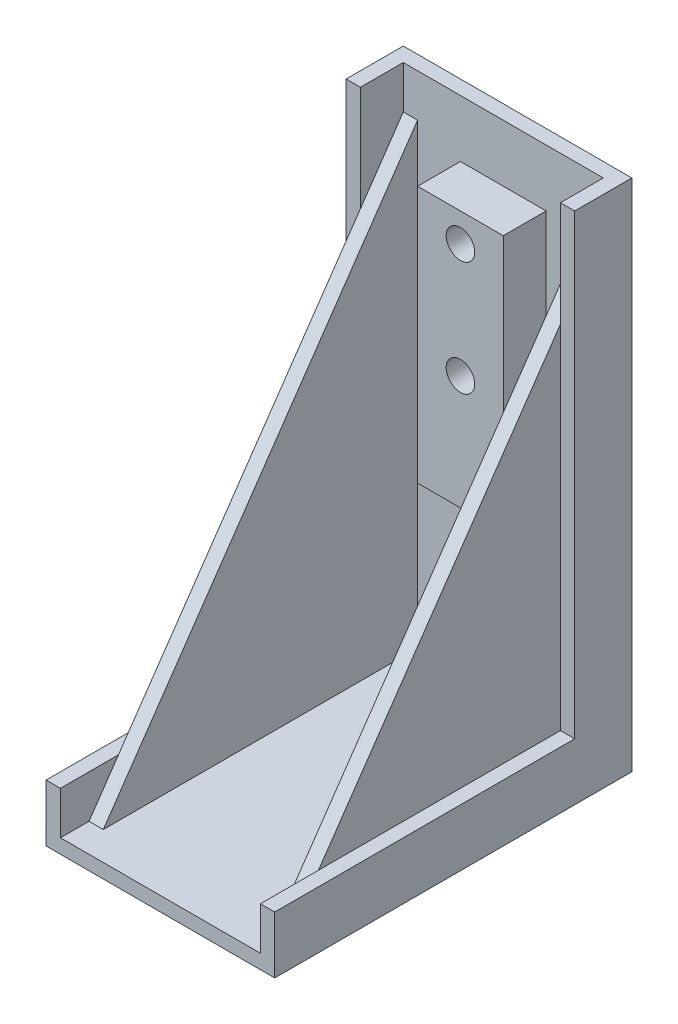
SolidWorks part; units mm, degrees
ref_plane "Front Plane" through (0, 0, 0) normal (0, 0, 1) x (1, 0, 0)
ref_plane "Top Plane" through (0, 0, 0) normal (0, 1, 0) x (1, 0, 0)
ref_plane "Right Plane" through (0, 0, 0) normal (1, 0, 0) x (0, 0, -1)
sketch "Sketch1" plane through (0, 0, 0) normal (0, 1, 0) x (1, 0, 0)
  line L1 (10, -13.75) -> (-10, -13.75)
  line L2 (10, -13.75) -> (10, 17.5)
  line L3 (10, 17.5) -> (-10, 17.5)
  line L4 (-10, -13.75) -> (-10, 17.5)
  point P0 (0, 0)
  dimension "D1" = 20
  dimension "D2" = 31.25
extrude "Boss-Extrude1" add sketch "Sketch1" along normal mid plane 5
sketch "Sketch2" plane through (0, 2.5, 0) normal (0, 1, 0) x (1, 0, 0)
  line L0 (-8.75, -12.5) -> (-8.75, -13.75)
  line L1 (-10, -13.75) -> (10, -13.75) construction
  line L2 (8.75, -12.5) -> (8.75, 16.25)
  line L3 (8.75, 16.25) -> (-8.75, 16.25)
  line L4 (-8.75, -12.5) -> (-8.75, 16.25)
  line L5 (-8.75, -13.75) -> (8.75, -13.75)
  line L6 (8.75, -13.75) -> (8.75, -12.5)
  point P0 (0, 0)
  dimension "D1" = 1.25
  dimension "D2" = 1.25
  dimension "D3" = 1.25
extrude "Cut-Extrude1" cut sketch "Sketch2" against normal blind 3.75
sketch "Sketch3" plane through (0, 2.5, 0) normal (0, 1, 0) x (1, 0, 0)
  line L0 (-8.737, 16.25) -> (-8.75, 12.5)
  line L1 (10, 17.5) -> (-10, 17.5) construction
  line L2 (-8.75, 16.25) -> (-8.75, -13.75) construction
  line L3 (-8.75, 12.5) -> (-10, 12.5)
  line L4 (-10, 17.5) -> (-10, -13.75) construction
  line L5 (-10, 12.5) -> (-10, 17.5)
  line L6 (-10, 17.5) -> (-8.7326, 17.5)
  line L7 (-10, 17.5) -> (10, 17.5)
  line L8 (10, 17.5) -> (10, 12.5)
  line L9 (10, -13.75) -> (10, 17.5) construction
  line L10 (10, 12.5) -> (8.75, 12.5)
  line L11 (8.75, -13.75) -> (8.75, 16.25) construction
  line L12 (8.75, 12.5) -> (8.75, 16.25)
  line L13 (8.75, 16.25) -> (-8.75, 16.25) construction
  line L14 (8.75, 16.25) -> (-8.75, 16.25)
  line M1 (8.75, 16.25) -> (8.75, -13.75)
  line M3 (10, -13.75) -> (10, 17.5)
  line M4 (10, 17.5) -> (-10, 17.5)
  line M5 (-10, 17.5) -> (-10, -13.75)
  line M7 (-8.75, -13.75) -> (-8.75, 16.25)
  line M8 (-8.75, 16.25) -> (8.75, 16.25)
extrude "Boss-Extrude2" add sketch "Sketch3" along normal blind 40 contours L10 L3 M3 M4 M5 M7 M8 M1
sketch "Sketch4" plane through (0, -1.25, 0) normal (0, 1, 0) x (1, 0, 0)
  line L2 (8.75, 16.25) -> (7.5, 16.25)
  line L3 (8.75, 16.25) -> (8.75, -11.25)
  line L4 (8.75, -11.25) -> (7.5, -11.25)
  line L5 (7.5, 16.25) -> (7.5, -11.25)
  line L6 (-8.75, 16.25) -> (-7.5, 16.25)
  line L8 (-8.75, 16.25) -> (-8.75, -11.25)
  line L9 (-8.75, -11.25) -> (-7.5, -11.25)
  line L10 (-7.5, 16.25) -> (-7.5, -11.25)
  dimension "D1" = 1.25
  dimension "D2" = 1.25
extrude "Boss-Extrude3" add sketch "Sketch4" along normal blind 40
sketch "Sketch7" plane through (7.5, 0, 0) normal (-1, 0, 0) x (0, 0, 1)
  line L0 (-16.25, 38.75) -> (11.25, 38.75)
  line L1 (-16.25, 38.75) -> (11.25, 38.75) construction
  line L2 (-16.25, 38.75) -> (11.25, -1.25)
  line L3 (11.25, -1.25) -> (11.25, 38.75)
extrude "Cut-Extrude5" cut sketch "Sketch7" against normal blind 1.25 and the other way blind 16.25
sketch "Sketch10" plane through (0, 0, -16.25) normal (0, 0, 1) x (1, 0, 0)
  circle A0 centre (0, 35) radius 1.25
  circle A1 centre (0, 25) radius 1.25
  point P8 (0, 42.5)
  dimension "D1" = 2
extrude "Cut-Extrude6" cut sketch "Sketch10" against normal through all and the other way blind 45.75
sketch "Sketch11" plane through (0, 0, -16.25) normal (0, 0, 1) x (1, 0, 0)
  line L1 (-3.75, 37.5) -> (3.75, 37.5)
  line L2 (3.75, 37.5) -> (3.75, 15)
  line L3 (-3.75, 37.5) -> (-3.75, 15)
  line L4 (-3.75, 15) -> (3.75, 15)
  point P7 (0, 37.5)
extrude "Boss-Extrude4" add sketch "Sketch11" along normal blind 3.75
sketch "Sketch12" plane through (0, 0, -17.5) normal (0, 0, -1) x (-1, 0, 0)
  circle A0 centre (0, 35) radius 1.25
  circle A1 centre (0, 25) radius 1.25
extrude "Cut-Extrude7" cut sketch "Sketch12" against normal blind 13.75
